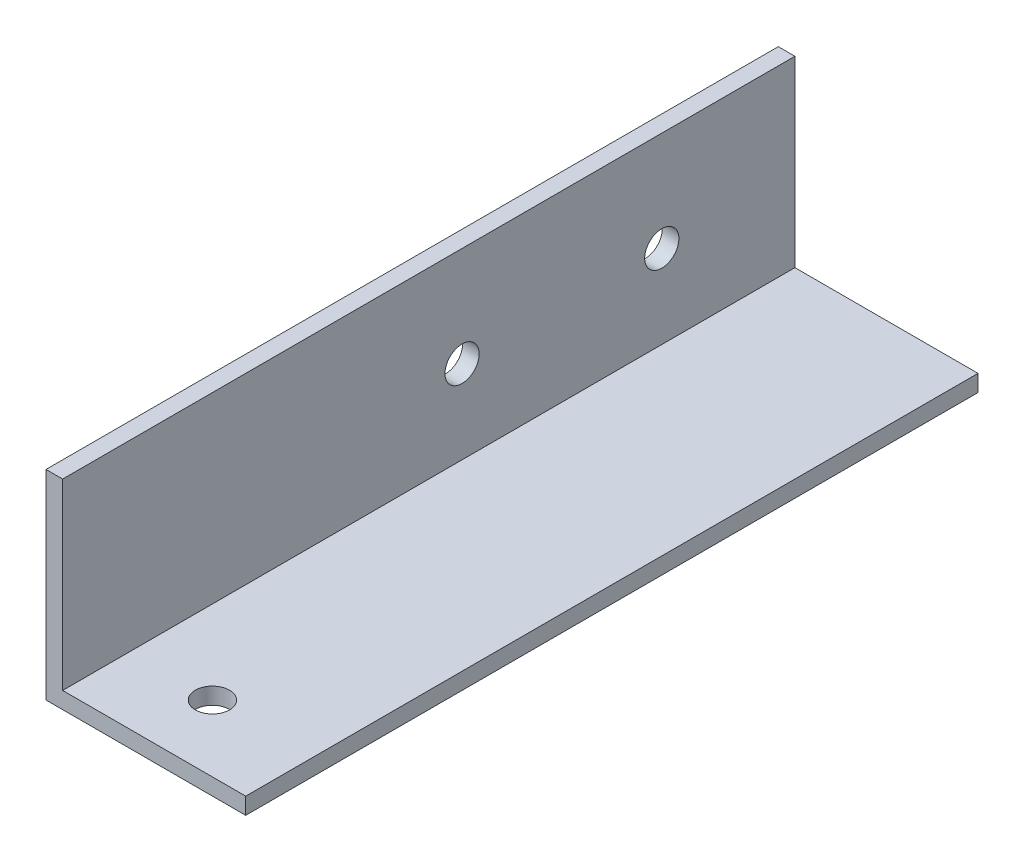
SolidWorks part; units mm, degrees
material "6061-T6 (SS)"
ref_plane "Front Plane" through (0, 0, 0) normal (0, 0, 1) x (1, 0, 0)
ref_plane "Top Plane" through (0, 0, 0) normal (0, 1, 0) x (1, 0, 0)
ref_plane "Right Plane" through (0, 0, 0) normal (1, 0, 0) x (0, 0, -1)
sketch "Sketch1" plane through (0, 0, 0) normal (0, 0, 1) x (1, 0, 0)
  line L0 (0, 0) -> (0, 19.05)
  line L1 (0, 19.05) -> (1.5875, 19.05)
  line L2 (1.5875, 19.05) -> (1.5875, 1.5875)
  line L3 (1.5875, 1.5875) -> (19.05, 1.5875)
  line L4 (19.05, 1.5875) -> (19.05, 0)
  line L5 (19.05, 0) -> (0, 0)
  dimension "D1" = 19.05
  dimension "D2" = 1.5875
extrude "Boss-Extrude1" add sketch "Sketch1" along normal blind 69.85
hole_wizard "#4 Clearance Hole1" positions "Sketch3" profile "Sketch2" hole size "#4" standard "ANSI Inch" end condition through all
sketch "Sketch3" plane through (1.5875, 0, 0) normal (1, 0, 0) x (0, 0, -1)
  line L0 (0, 1.5875) -> (0, 19.05) construction
  line L2 (-69.85, 19.05) -> (0, 19.05) construction
  point P0 (-12.7, 9.525)
  point P15 (-31.75, 9.525)
  dimension "D1" = 12.7
  dimension "D2" = 9.525
  dimension "D3" = 19.05
  dimension "D4" = 9.525
sketch "Sketch2" plane through (1.5875, 9.525, 12.7) normal (0, 1, 0) x (0, 0, -1)
  line L0 (0, 0) -> (0, 1.5875)
  line L1 (0, 1.5875) -> (1.6319, 1.5875)
  line L2 (1.6319, 1.5875) -> (1.6319, 0)
  line L5 (1.6319, 0) -> (0, 0)
  line L11 (0, -6.35) -> (0, 107.95) construction
  dimension "Thru Hole Dia." = 3.2639
  dimension "Thru Hole Depth" = 1.5875
hole_wizard "#4 Clearance Hole2" positions "Sketch5" profile "Sketch4" hole size "#4" standard "ANSI Inch" end condition through all
sketch "Sketch5" plane through (0, 1.5875, 0) normal (0, 1, 0) x (1, 0, 0)
  line L0 (19.05, -69.85) -> (1.5875, -69.85) construction
  line L1 (19.05, -69.85) -> (19.05, 0) construction
  point P0 (9.525, -63.5)
  dimension "D1" = 6.35
  dimension "D2" = 9.525
sketch "Sketch4" plane through (9.525, 1.5875, 63.5) normal (1, 0, 0) x (0, 0, 1)
  line L0 (0, 0) -> (0, 1.5875)
  line L1 (0, 1.5875) -> (1.6319, 1.5875)
  line L2 (1.6319, 1.5875) -> (1.6319, 0)
  line L5 (1.6319, 0) -> (0, 0)
  line L11 (0, -6.35) -> (0, 107.95) construction
  dimension "Thru Hole Dia." = 3.2639
  dimension "Thru Hole Depth" = 1.5875
